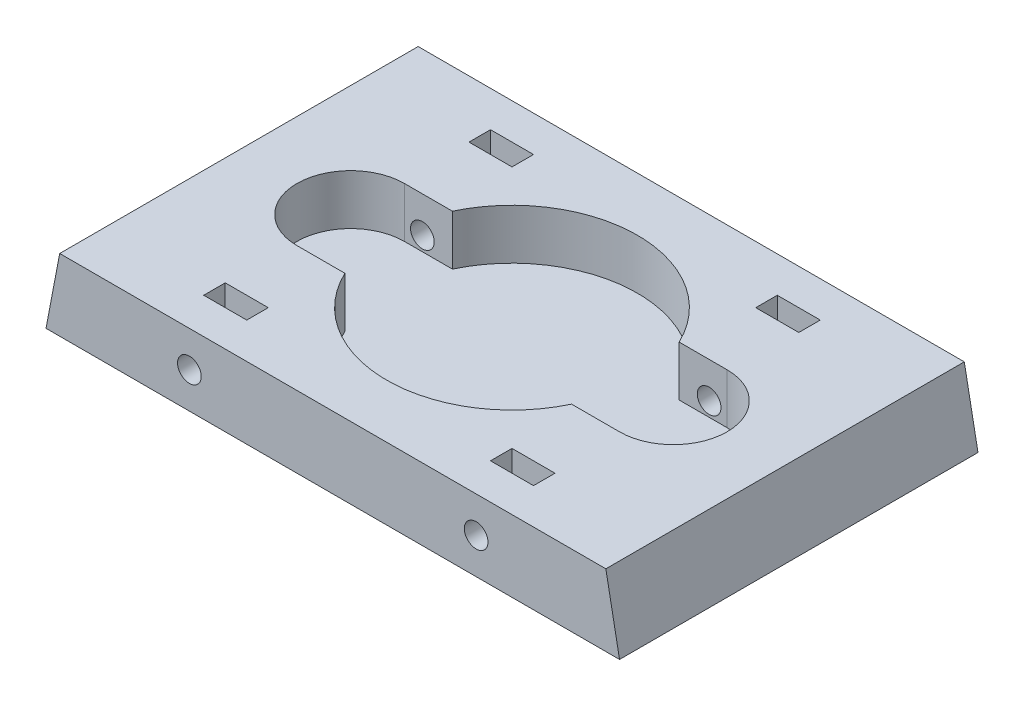
SolidWorks part; units mm, degrees
ref_plane "Front Plane" through (0, 0, 0) normal (0, 0, 1) x (1, 0, 0)
ref_plane "Top Plane" through (0, 0, 0) normal (0, 1, 0) x (1, 0, 0)
ref_plane "Right Plane" through (0, 0, 0) normal (1, 0, 0) x (0, 0, -1)
sketch "Sketch1" plane through (0, 0, 0) normal (0, 1, 0) x (1, 0, 0)
  line L1 (-40, 25) -> (40, 25)
  line L2 (-40, 25) -> (-40, -25)
  line L3 (-40, -25) -> (40, -25)
  line L4 (40, 25) -> (40, -25)
  line L5 (-40, 25) -> (40, -25) construction
  line L6 (-40, -25) -> (40, 25) construction
  point P0 (0, 0)
  dimension "D1" = 80
  dimension "D2" = 50
extrude "Boss-Extrude1" add sketch "Sketch1" along normal mid plane 10
sketch "Sketch3" plane through (0, 0, 25) normal (0, 0, 1) x (1, 0, 0)
  circle A0 centre (-20, 0) radius 1.65
  dimension "D2" = 3.3
  dimension "D1" = 20
extrude "Cut-Extrude1" cut sketch "Sketch3" against normal blind 5
sketch "Sketch4" plane through (0, 0, 20) normal (0, 0, 1) x (1, 0, 0)
  line L0 (-23, 1.7321) -> (-23, 5.7575)
  line L2 (-23, 1.7321) -> (-23, -1.7321)
  line L3 (-23, -1.7321) -> (-20, -3.4641)
  line L4 (-20, -3.4641) -> (-17, -1.7321)
  line L5 (-17, -1.7321) -> (-17, 1.7321)
  line L7 (-23, 5.7575) -> (-17, 5.7575)
  line L8 (-17, 5.7575) -> (-17, 1.7321)
  line L10 (-21.5, 2.5981) -> (-23, 1.7321) [skipped]
  line L11 (-17, 1.7321) -> (-18.5, 2.5981) [skipped]
  circle A0 centre (-20, 0) radius 3 construction
  dimension "D1" = 6
extrude "Cut-Extrude2" cut sketch "Sketch4" against normal blind 3
sketch "Sketch5" plane through (0, 0, 17) normal (0, 0, 1) x (1, 0, 0)
  circle A0 centre (-20, 0) radius 1.65
  dimension "D1" = 3.3
extrude "Cut-Extrude3" cut sketch "Sketch5" against normal blind 10
mirror "Mirror1" about plane through (0, 0, 0) normal (1, 0, 0) of "Cut-Extrude3", "Cut-Extrude2", "Cut-Extrude1"
mirror "Mirror2" about plane through (0, 0, 0) normal (0, 0, 1) of "Mirror1", "Cut-Extrude1", "Cut-Extrude2", "Cut-Extrude3"
sketch "Sketch6" plane through (0, 0, 25) normal (0, 0, 1) x (1, 0, 0)
  line L0 (-40, 5) -> (-38.09, 5)
  line L1 (-40, 5) -> (40, 5) construction
  line L2 (-38.09, 5) -> (-40, -5)
  line L3 (-40, -5) -> (-40, 5)
  dimension "D1" = 1.91
extrude "Cut-Extrude4" cut sketch "Sketch6" against normal through all
mirror "Mirror3" about plane through (0, 0, 0) normal (1, 0, 0) of "Cut-Extrude4"
sketch "Sketch7" plane through (0, 5, 0) normal (0, 1, 0) x (1, 0, 0)
  circle A0 centre (0, 0) radius 17.5
  dimension "D1" = 35
extrude "Cut-Extrude5" cut sketch "Sketch7" against normal blind 7
sketch "Sketch8" plane through (0, 5, 0) normal (0, 1, 0) x (1, 0, 0)
  line L0 (22.5, 0) -> (-22.5, 0) construction
  line L1 (22.5, -7.5) -> (-22.5, -7.5)
  line L2 (22.5, 7.5) -> (-22.5, 7.5)
  arc A0 (22.5, -7.5) -> (22.5, 7.5) centre (22.5, 0) ccw
  arc A1 (-22.5, 7.5) -> (-22.5, -7.5) centre (-22.5, 0) ccw
  point P2 (0, 0)
  dimension "D1" = 45
  dimension "D2" = 15
extrude "Cut-Extrude6" cut sketch "Sketch8" against normal blind 7
